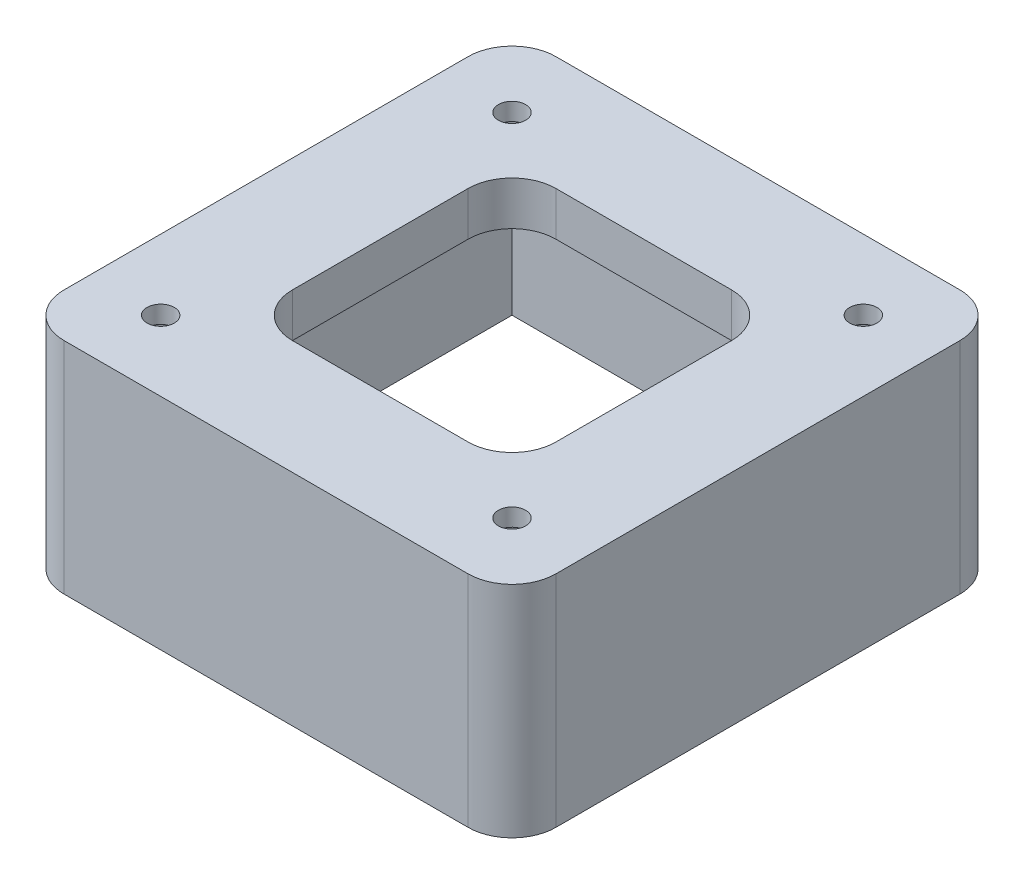
SolidWorks part; units mm, degrees
material "ABS"
ref_plane "Front Plane" through (0, 0, 0) normal (0, 0, 1) x (1, 0, 0)
ref_plane "Top Plane" through (0, 0, 0) normal (0, 1, 0) x (1, 0, 0)
ref_plane "Right Plane" through (0, 0, 0) normal (1, 0, 0) x (0, 0, -1)
sketch "Sketch1" plane through (0, 0, 0) normal (0, 1, 0) x (1, 0, 0)
  line L1 (-20, -20) -> (20, -20) construction
  line L2 (-20, -20) -> (-20, 20) construction
  line L3 (-20, 20) -> (20, 20) construction
  line L4 (20, -20) -> (20, 20) construction
  line L5 (-20, -20) -> (20, 20) construction
  line L6 (-20, 20) -> (20, -20) construction
  line L7 (28, -28) -> (-28, -28)
  line L8 (28, -28) -> (28, 28)
  line L9 (28, 28) -> (-28, 28)
  line L10 (-28, -28) -> (-28, 28)
  line L11 (28, -28) -> (-28, 28) construction
  line L12 (28, 28) -> (-28, -28) construction
  line L13 (-15, -15) -> (15, -15)
  line L14 (-15, -15) -> (-15, 15)
  line L15 (-15, 15) -> (15, 15)
  line L16 (15, -15) -> (15, 15)
  line L17 (-15, -15) -> (15, 15) construction
  line L18 (-15, 15) -> (15, -15) construction
  circle A0 centre (-20, 20) radius 1.55
  circle A1 centre (20, 20) radius 1.55
  circle A2 centre (20, -20) radius 1.55
  circle A3 centre (-20, -20) radius 1.55
  point P0 (0, 0)
  point P10 (0, 0)
  point P15 (0, 0)
  dimension "D7" = 3.1
  dimension "D8" = 3.1
  dimension "D9" = 3.1
  dimension "D10" = 3.1
  dimension "D1" = 40
  dimension "D2" = 40
  dimension "D3" = 56
  dimension "D4" = 56
  dimension "D5" = 30
  dimension "D6" = 30
extrude "Boss-Extrude1" add sketch "Sketch1" along normal blind 5
sketch "Sketch2" plane through (0, 0, 0) normal (0, -1, 0) x (1, 0, 0)
  circle A81 centre (-20, 20) radius 3.55
  circle A82 centre (-20, 20) radius 3.55
  circle A84 centre (20, 20) radius 3.55
  circle A85 centre (20, 20) radius 3.55
  circle A87 centre (-20, -20) radius 3.55
  circle A88 centre (-20, -20) radius 3.55
  circle A90 centre (20, -20) radius 3.55
  circle A91 centre (20, -20) radius 3.55
  dimension "D1" = 2
  dimension "D2" = 2
  dimension "D3" = 2
  dimension "D4" = 2
extrude "Cut-Extrude1" cut sketch "Sketch2" against normal blind 3
fillet "Fillet1" radius 5 4 edges at (-15, 2.5, -15) (15, 2.5, -15) (15, 2.5, 15) (-15, 2.5, 15)
sketch "Sketch3" plane through (0, 0, 0) normal (0, -1, 0) x (1, 0, 0)
  line L12 (-25, 25) -> (-25, -25)
  line L13 (-25, -25) -> (25, -25)
  line L14 (25, -25) -> (25, 25)
  line L15 (25, 25) -> (-25, 25)
  line L16 (-28, 28) -> (-28, -28)
  line L17 (-28, -28) -> (28, -28)
  line L18 (28, -28) -> (28, 28)
  line L19 (28, 28) -> (-28, 28)
  line L20 (-28, 28) -> (-28, -28)
  line L21 (-28, -28) -> (28, -28)
  line L22 (28, -28) -> (28, 28)
  line L23 (28, 28) -> (-28, 28)
  dimension "D1" = 50
  dimension "D3" = 50
  dimension "D2" = 0
extrude "Boss-Extrude2" add sketch "Sketch3" along normal blind 20
fillet "Fillet2" radius 5 4 edges at (28, -7.5, 28) (28, -7.5, -28) (-28, -7.5, -28) (-28, -7.5, 28)
equation "\"D3@Sketch3\"=\"D1@Sketch3\""
equation "\"D8@Sketch1\"=\"D7@Sketch1\""
equation "\"D9@Sketch1\"=\"D8@Sketch1\""
equation "\"D10@Sketch1\"=\"D9@Sketch1\""
